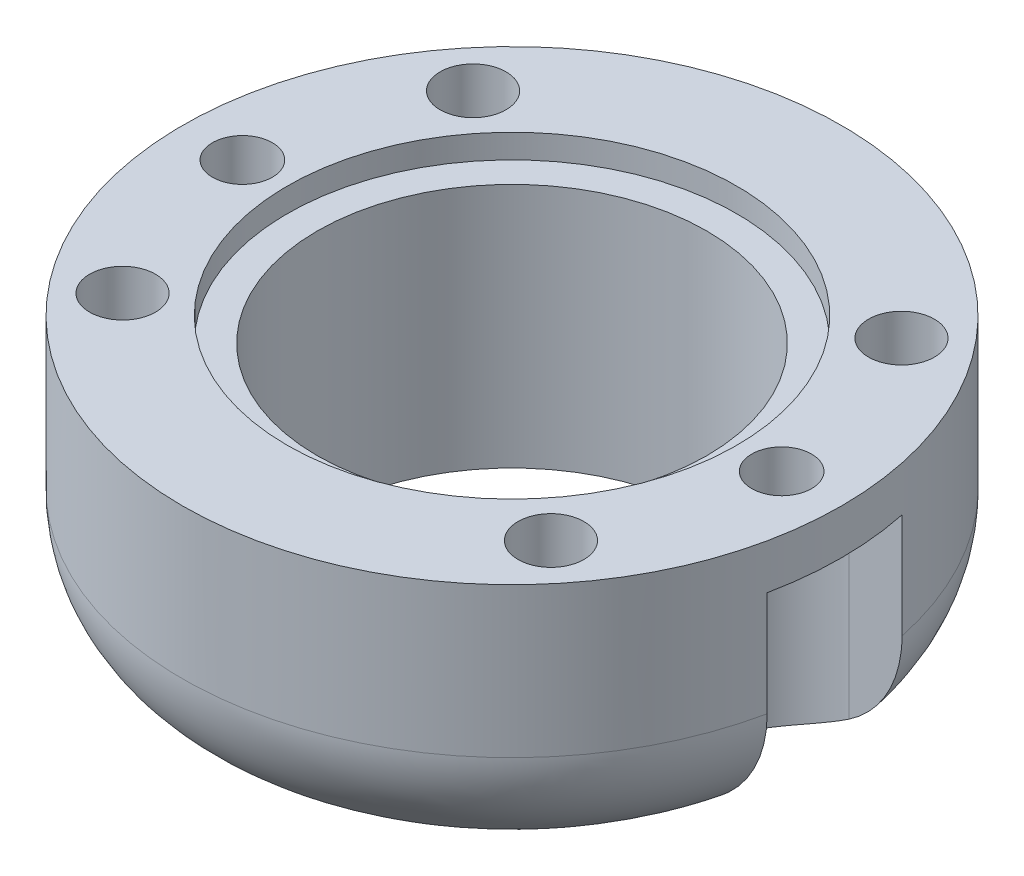
SolidWorks part; units mm, degrees
ref_plane "Front Plane" through (0, 0, 0) normal (0, 0, 1) x (1, 0, 0)
ref_plane "Top Plane" through (0, 0, 0) normal (0, 1, 0) x (1, 0, 0)
ref_plane "Right Plane" through (0, 0, 0) normal (1, 0, 0) x (0, 0, -1)
sketch "Sketch1" plane through (0, 0, 0) normal (0, 1, 0) x (1, 0, 0)
  line L0 (-11, 0) -> (-11, 22.01)
  line L1 (-0.01, 33) -> (0.01, 33)
  line L2 (11, 22.01) -> (11, 0)
  circle A1 centre (0, 0) radius 11 construction
  circle A2 centre (0, 0) radius 6.5
  arc A3 (-11, 0) -> (11, 0) centre (0, 0) ccw
  arc A4 (11, 22.01) -> (0.01, 33) centre (0.01, 22.01) ccw
  arc A5 (-11, 22.01) -> (-0.01, 33) centre (-0.01, 22.01) cw
  dimension "D1" = 13
  dimension "D2" = 22
  dimension "D4" = 10.99
  dimension "D3" = 33
extrude "Boss-Extrude1" add sketch "Sketch1" along normal blind 9
sketch "Sketch2" plane through (0, 9, 0) normal (0, 1, 0) x (1, 0, 0)
  line L0 (-11, 0) -> (11, 0) construction
  line L2 (0, 6.5) -> (0, 0) construction
  circle A1 centre (-7.15, 5.85) radius 1.1
  circle A2 centre (-7.15, -5.85) radius 1.1
  circle A5 centre (0, 0) radius 6.5 construction
  circle A6 centre (7.15, -5.85) radius 1.1
  circle A7 centre (7.15, 5.85) radius 1.1
  arc A8 (-11, 0) -> (11, 0) centre (0, 0) ccw construction
  dimension "D1" = 2.2
  dimension "D2" = 7.15
  dimension "D3" = 5.85
extrude "Cut-Extrude1" cut sketch "Sketch2" against normal blind 3
sketch "Sketch3" plane through (0, 9, 0) normal (0, 1, 0) x (1, 0, 0)
  line L0 (-11, 0) -> (11, 0) construction
  line L2 (0, 6.5) -> (0, 0) construction
  circle A0 centre (-9, 0) radius 1
  circle A1 centre (9, 0) radius 1
  dimension "D1" = 2
  dimension "D4" = 2
  dimension "D2" = 9
  dimension "D3" = 9
extrude "Cut-Extrude2" cut sketch "Sketch3" against normal blind 20 contours A0
sketch "Sketch4" plane through (0, 0, 0) normal (0, -1, 0) x (1, 0, 0)
  line L0 (-9, 2.25) -> (-10.7674, 2.25)
  line L1 (-9, -2.25) -> (-11, -2.25)
  line L2 (-11, -2.25) -> (-12, 0)
  line L3 (-12, 0) -> (-10.7674, 2.25)
  line L4 (-11, 0) -> (11, 0) construction
  line L6 (0, 6.5) -> (0, 0) construction
  line L11 (-11, -22.01) -> (-11, 0) construction
  line L12 (12, 0) -> (10.7674, 2.25)
  line L13 (11, -2.25) -> (12, 0)
  line L14 (9, -2.25) -> (11, -2.25)
  line L15 (9, 2.25) -> (10.7674, 2.25)
  circle A0 centre (-9, 0) radius 2.25 construction
  arc A3 (-9, 2.25) -> (-9, -2.25) centre (-9, 0) cw
  arc A5 (11, 0) -> (-11, 0) centre (0, 0) ccw construction
  arc A6 (9, 2.25) -> (9, -2.25) centre (9, 0) ccw
  circle A7 centre (0, 0) radius 6.5 construction
  dimension "D1" = 4.5
  dimension "D2" = 1
extrude "Cut-Extrude3" cut sketch "Sketch4" against normal blind 7.5 contours L0 L3 L2 L1 A3
sketch "Sketch6" plane through (0, 0, 0) normal (0, -1, 0) x (1, 0, 0)
  line L0 (0, -6.5) -> (0, -33) construction
  line L1 (0.01, -33) -> (-0.01, -33) construction
  line L3 (-11, -22.01) -> (11, -22.01) construction
  line L4 (-3.4, -25.41) -> (3.4, -25.41)
  line L5 (-3.4, -25.41) -> (-3.4, -18.61)
  line L6 (-3.4, -18.61) -> (3.4, -18.61)
  line L7 (3.4, -25.41) -> (3.4, -18.61)
  line L8 (-3.4, -25.41) -> (3.4, -18.61) construction
  line L9 (-3.4, -18.61) -> (3.4, -25.41) construction
  point P5 (0, -22.01)
  dimension "D1" = 6.8
  dimension "D2" = 6.8
extrude "Cut-Extrude4" cut sketch "Sketch6" against normal blind 5
sketch "Sketch7" plane through (0, 5, 0) normal (0, -1, 0) x (1, 0, 0)
  line L0 (0, -18.61) -> (0, -25.41) construction
  line L1 (3.4, -18.61) -> (-3.4, -18.61) construction
  line L2 (-3.4, -25.41) -> (3.4, -25.41) construction
  line L3 (-3.4, -22.01) -> (3.4, -22.01) construction
  line L4 (-3.4, -18.61) -> (-3.4, -25.41) construction
  line L5 (3.4, -25.41) -> (3.4, -18.61) construction
  line L6 (3.4, -18.61) -> (1, -18.61)
  line L7 (-3.4, -18.61) -> (-1, -18.61)
  line L8 (-3.4, -18.61) -> (-3.4, -21.01)
  line L9 (-3.4, -21.01) -> (-1, -21.01)
  line L10 (-1, -18.61) -> (-1, -21.01)
  line L11 (3.4, -18.61) -> (3.4, -21.01)
  line L12 (3.4, -21.01) -> (1, -21.01)
  line L13 (1, -18.61) -> (1, -21.01)
  line L14 (3.4, -25.41) -> (1, -25.41)
  line L15 (3.4, -25.41) -> (3.4, -23.01)
  line L16 (3.4, -23.01) -> (1, -23.01)
  line L17 (1, -25.41) -> (1, -23.01)
  line L18 (-3.4, -25.41) -> (-1, -25.41)
  line L19 (-3.4, -25.41) -> (-3.4, -23.01)
  line L20 (-3.4, -23.01) -> (-1, -23.01)
  line L21 (-1, -25.41) -> (-1, -23.01)
  dimension "D1" = 1
  dimension "D2" = 1
extrude "Cut-Extrude5" cut sketch "Sketch7" against normal blind 5
fillet "Fillet2" radius 4 1 edges at (0, 0, 11)
sketch "Sketch8" plane through (0, 0, 0) normal (0, -1, 0) x (1, 0, 0)
  line L0 (-11, -22.01) -> (11, -22.01) construction
  line L1 (-9, 0) -> (-9, -22.01) construction
  line L2 (0, -18.61) -> (0, -25.41) construction
  line L3 (3.4, -18.61) -> (-3.4, -18.61) construction
  line L4 (-1, -25.41) -> (1, -25.41) construction
  circle A0 centre (-9, -22.01) radius 1
  circle A1 centre (9, -22.01) radius 1
  dimension "D1" = 2
extrude "Cut-Extrude6" cut sketch "Sketch8" against normal blind 20
sketch "Sketch9" plane through (0, 9, 0) normal (0, 1, 0) x (1, 0, 0)
  circle A0 centre (0, 0) radius 7.5
  circle A1 centre (0, 0) radius 6.5 construction
  dimension "D1" = 1
extrude "Cut-Extrude7" cut sketch "Sketch9" against normal blind 0.8
sketch "Sketch11" plane through (3.4, 0, 0) normal (-1, 0, 0) x (0, 0, 1)
  line L0 (-23.01, 9) -> (-25.41, 9) construction
  line L5 (-16.6851, 9) -> (-11.6851, 9)
  line L6 (-16.6851, 9) -> (-16.6851, 8)
  line L7 (-16.6851, 8) -> (-11.6851, 8)
  line L8 (-11.6851, 9) -> (-11.6851, 8)
  line L9 (-6.6851, 9) -> (-6.6851, 8.2) construction
  dimension "D1" = 5
  dimension "D2" = 1
  dimension "D3" = 5
extrude "Boss-Extrude2" add sketch "Sketch11" along normal blind 5
sketch "Sketch12" plane through (0, 0, 0) normal (0, -1, 0) x (1, 0, 0)
  line L1 (-23.8497, 14.9277) -> (29.1567, 14.9277)
  line L2 (-23.8497, 14.9277) -> (-23.8497, -39.1017)
  line L3 (-23.8497, -39.1017) -> (29.1567, -39.1017)
  line L4 (29.1567, 14.9277) -> (29.1567, -39.1017)
  circle A0 centre (0, 0) radius 11
  arc A1 (10.7674, 2.25) -> (-10.7674, 2.25) centre (0, 0) ccw construction
extrude "Cut-Extrude9" cut sketch "Sketch12" against normal blind 10 contours L4 L3 L2 L1
fillet "Fillet3" radius 4 1 edges at (0, 0, -11)
